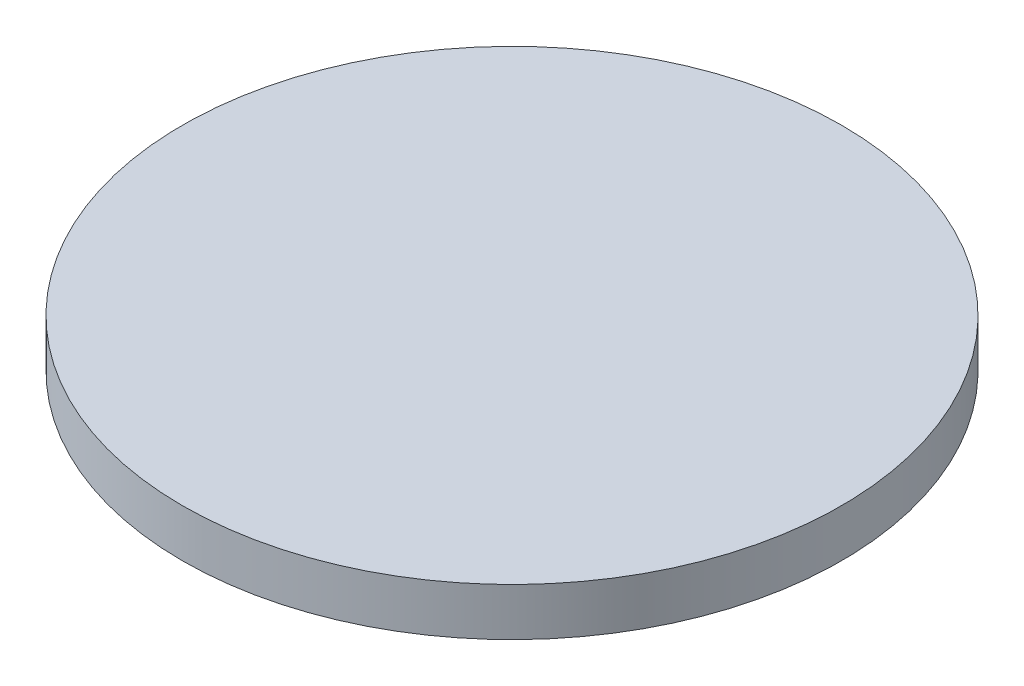
SolidWorks part; units mm, degrees
ref_plane "Спереди" through (0, 0, 0) normal (0, 0, 1) x (1, 0, 0)
ref_plane "Сверху" through (0, 0, 0) normal (0, 1, 0) x (1, 0, 0)
ref_plane "Справа" through (0, 0, 0) normal (1, 0, 0) x (0, 0, -1)
sketch "Эскиз1" plane through (0, 0, 0) normal (0, 1, 0) x (1, 0, 0)
  circle A0 centre (0, 0) radius 69
extrude "Бобышка-Вытянуть1" add sketch "Эскиз1" along normal blind 10
